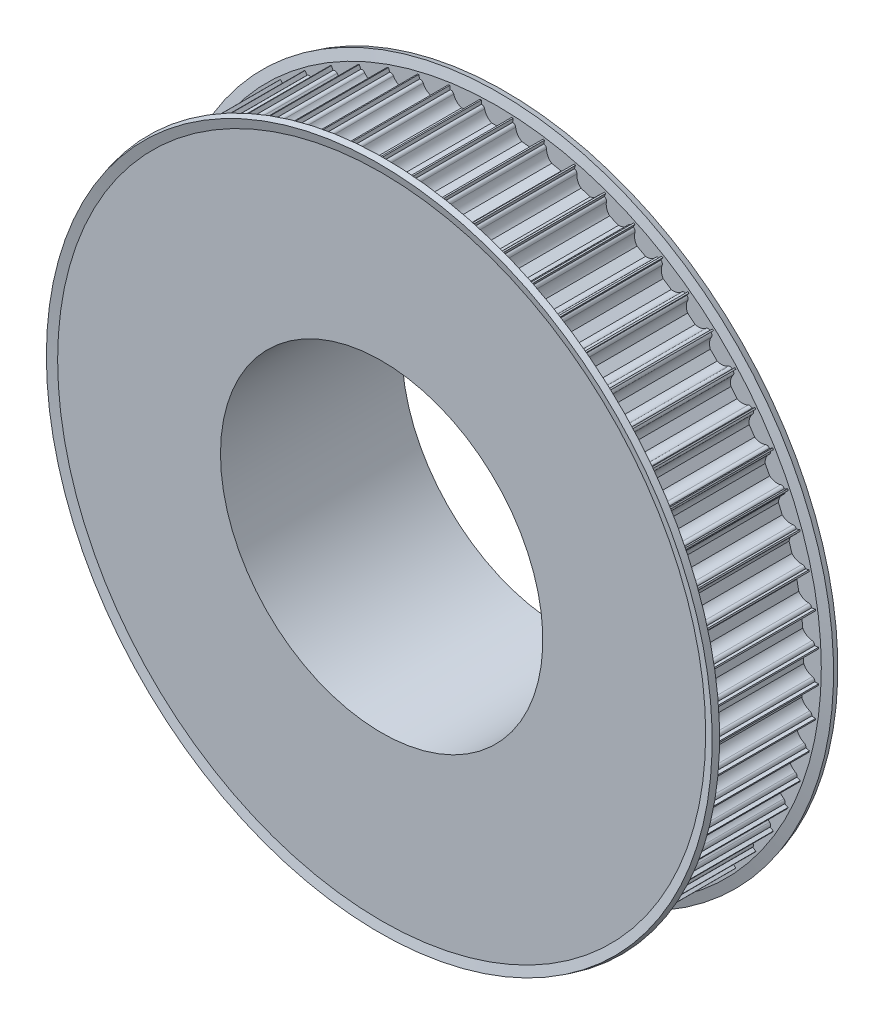
SolidWorks part; units mm, degrees
ref_plane "Alzado" through (0, 0, 0) normal (0, 0, 1) x (1, 0, 0)
ref_plane "Planta" through (0, 0, 0) normal (0, 1, 0) x (1, 0, 0)
ref_plane "Vista lateral" through (0, 0, 0) normal (1, 0, 0) x (0, 0, -1)
ref_axis "Eje1" through (0, 0, -88.99) along (0, 0, 1)
sketch "Croquis1" plane through (0, 0, 0) normal (1, 0, 0) x (0, 0, -1)
  line L0 (0, 40) -> (0, 80)
  line L1 (0, 80) -> (30, 80)
  line L2 (30, 80) -> (30, 55.5)
  line L3 (30, 55.5) -> (45, 55.5)
  line L4 (45, 55.5) -> (45, 40)
  line L5 (45, 40) -> (0, 40)
  line L6 (88.99, 0) -> (-88.99, 0) construction
  dimension "D1" = 40
  dimension "D2" = 40
  dimension "D3" = 30
  dimension "D4" = 15
  dimension "D5" = 15.5
revolve "Revolución1" add sketch "Croquis1" angle 360 about axis through (0, 0, -88.99) along (0, 0, 1)
sketch "Croquis2" plane through (0, 0, 0) normal (0, 0, 1) x (1, 0, 0)
  line L0 (3.6742, 79) -> (3.75, 79)
  line L1 (-3.75, 81) -> (3.75, 81)
  line L2 (-3.75, 81) -> (-3.75, 79)
  line L3 (-3.75, 79) -> (-3.6742, 79)
  line L4 (3.75, 81) -> (3.75, 79)
  line L5 (-1.199, 76.25) -> (1.199, 76.25)
  arc A0 (2.9394, 78.4) -> (1.199, 76.25) centre (0, 79) cw
  arc A1 (2.9394, 78.4) -> (3.6742, 79) centre (3.6742, 78.25) cw
  arc A2 (-2.9394, 78.4) -> (-3.6742, 79) centre (-3.6742, 78.25) ccw
  arc A3 (-1.199, 76.25) -> (-2.9394, 78.4) centre (0, 79) cw
  point P16 (3, 79)
  point P19 (-3, 79)
  dimension "D1" = 3
  dimension "D5" = 0.75
  dimension "D2" = 2
  dimension "D3" = 7.5
  dimension "D4" = 79
  dimension "D6" = 2.75
extrude "Cortar-Extruir1" cut sketch "Croquis2" against normal through all contours L1 L4 L0 A1 A0 L5 A3 A2 L3 L2
pattern_circular "MatrizC1" count 64 over 360 about axis through (0, 0, 0) along (0, 0, 1) of "Cortar-Extruir1"
sketch "Croquis4" plane through (0, 0, 0) normal (1, 0, 0) x (0, 0, -1)
  line L0 (0, -37.0014) -> (0, -39.5498) construction
  line L1 (0, 75.6121) -> (1.5, 75.6121)
  line L2 (0, 75.6121) -> (0, 80.6121)
  line L3 (0, 80.6121) -> (1.5, 80.6121) construction
  line L4 (1.5, 75.6121) -> (1.5, 80.6121)
  line L5 (30, 79.9121) -> (0, 79.9121) construction
  line L6 (1.5, 80.6121) -> (0.0511, 80.2238) construction
  line L7 (1.5, 80.6121) -> (0.8569, 83.0121)
  line L8 (0.0511, 80.2238) -> (-0.592, 82.6238)
  line L9 (0.8569, 83.0121) -> (-0.592, 82.6238)
  line L10 (15, 34.5922) -> (15, -37.4964) construction
  line L11 (28.5, 80.6121) -> (29.9489, 80.2238) construction
  line L12 (30, 80.6121) -> (28.5, 80.6121) construction
  line L13 (29.1431, 83.0121) -> (30.592, 82.6238)
  line L14 (29.9489, 80.2238) -> (30.592, 82.6238)
  line L15 (28.5, 80.6121) -> (29.1431, 83.0121)
  line L16 (28.5, 75.6121) -> (28.5, 80.6121)
  line L17 (30, 75.6121) -> (30, 80.6121)
  line L18 (30, 75.6121) -> (28.5, 75.6121)
  line L19 (30, -40.9775) -> (0, -40.9775) construction
  dimension "D1" = 1.5
  dimension "D2" = 5
  dimension "D3" = 1.5
  dimension "D4" = 165
  dimension "D5" = 2.4
  dimension "D6" = 0.7
revolve "Revolución2" add sketch "Croquis4" angle 360 about axis through (0, 0, -88.99) along (0, 0, 1)
